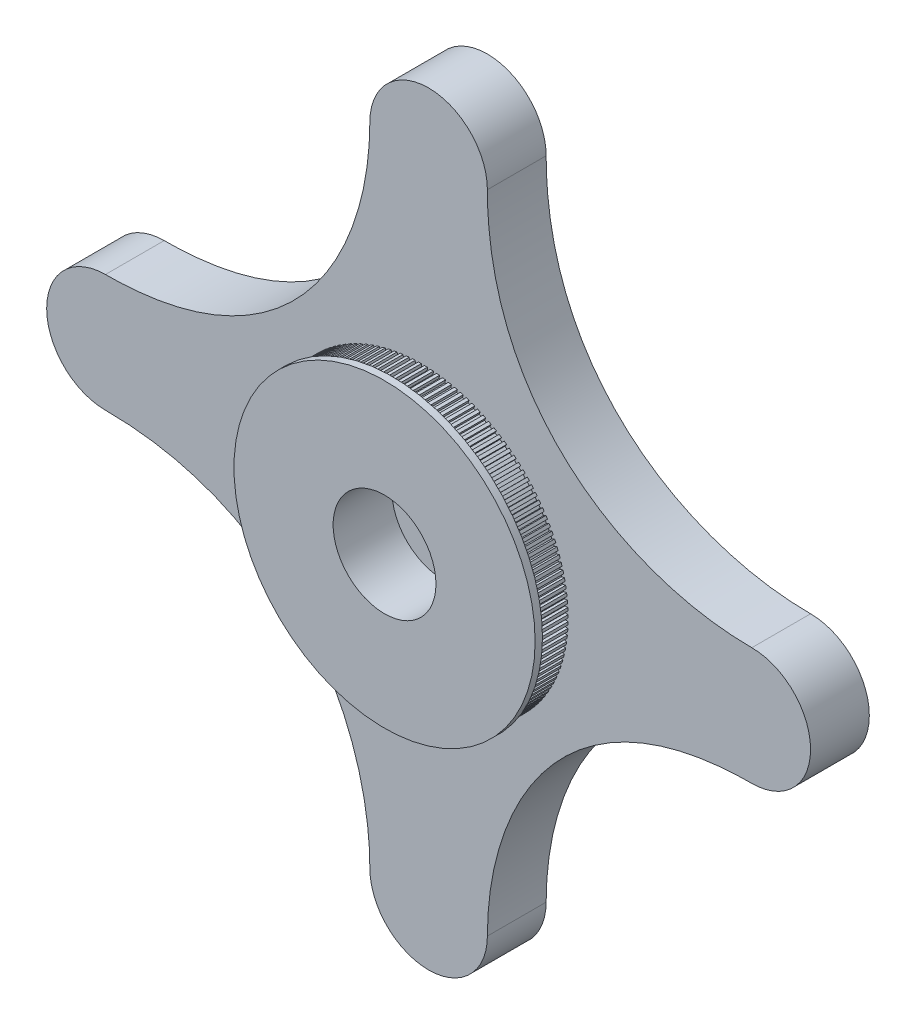
SolidWorks part; units mm, degrees
ref_plane "Front Plane" through (0, 0, 0) normal (0, 0, 1) x (1, 0, 0)
ref_plane "Top Plane" through (0, 0, 0) normal (0, 1, 0) x (1, 0, 0)
ref_plane "Right Plane" through (0, 0, 0) normal (1, 0, 0) x (0, 0, -1)
sketch "Sketch1" plane through (0, 0, 0) normal (0, 0, 1) x (1, 0, 0)
  line L0 (0, -50) -> (0, 50) construction
  line L1 (-50, 0) -> (50, 0) construction
  line L2 (-50, 0) -> (-110, 0) construction
  line L3 (0, 50) -> (0, 110) construction
  line L6 (50, 0) -> (90, 0) construction
  line L7 (0, -50) -> (0, -110) construction
  arc A6 (-20, -110) -> (20, -110) centre (0, -110) ccw
  arc A7 (20, 110) -> (-20, 110) centre (0, 110) ccw
  arc A8 (110, -20) -> (110, 20) centre (110, 0) ccw
  arc A9 (-110, 20) -> (-110, -20) centre (-110, 0) ccw
  spline S0 degree 3 poles (110, -20) (47.4794, -20) (20, -67.5736) (20, -110) knots 0 0 0 0 1 1 1 1
  spline S1 degree 3 poles (110, 20) (67.5736, 20) (20, 47.4794) (20, 110) knots 0 0 0 0 1 1 1 1
  spline S2 degree 3 poles (-20, 110) (-20, 67.5736) (-47.4794, 20) (-110, 20) knots 0 0 0 0 1 1 1 1
  spline S4 degree 3 poles (-110, -20) (-47.4794, -20) (-20, -67.5736) (-20, -110) knots 0 0 0 0 1 1 1 1
  dimension "D1" = 40
  dimension "D2" = 40
  dimension "D3" = 40
  dimension "D4" = 60
extrude "Boss-Extrude4" add sketch "Sketch1" along normal blind 20
sketch "Sketch5" plane through (0, 0, 0) normal (0, 0, -1) x (-1, 0, 0)
  circle A0 centre (0, 110) radius 7.5
  circle A1 centre (-110, 0) radius 7.5
  circle A2 centre (0, -110) radius 7.5
  circle A3 centre (110, 0) radius 7.5
  dimension "D1" = 15
extrude "Boss-Extrude5" add sketch "Sketch5" along normal blind 2.5
sketch "Sketch6" plane through (0, 0, 20) normal (0, 0, 1) x (1, 0, 0)
  circle A1 centre (0, 0) radius 45
  dimension "D2" = 90
extrude "Boss-Extrude7" add sketch "Sketch6" along normal blind 2.5
sketch "Sketch7" plane through (0, 0, 22.5) normal (0, 0, 1) x (1, 0, 0)
  circle A0 centre (0, 0) radius 50
  dimension "D1" = 100
extrude "Boss-Extrude8" add sketch "Sketch7" along normal blind 10
sketch "Sketch11" plane through (0, 0, 32.5) normal (0, 0, 1) x (1, 0, 0)
  line L0 (0, -49) -> (0, -49.9941)
  line L1 (1, -49.9841) -> (1, -48.9898)
  line L2 (-1.0664, -49.9828) -> (-2.066, -49.9514)
  line L3 (1, -49.9841) -> (0, -49.9941)
  line L4 (-1.0664, -49.9828) -> (-1.0254, -48.9893)
  line L5 (-2.0249, -48.9581) -> (-2.066, -49.9514)
  line L6 (-3.1311, -49.896) -> (-4.1285, -49.8234)
  line L7 (-3.1311, -49.896) -> (-3.049, -48.905)
  line L8 (-4.0464, -48.8326) -> (-4.1285, -49.8234)
  line L9 (-5.1903, -49.724) -> (-6.1839, -49.6102)
  line L10 (-5.1903, -49.724) -> (-5.0674, -48.7373)
  line L11 (-6.0609, -48.6237) -> (-6.1839, -49.6102)
  line L12 (-7.2408, -49.467) -> (-8.2288, -49.3123)
  line L13 (-7.2408, -49.467) -> (-7.0771, -48.4862)
  line L14 (-8.0651, -48.3317) -> (-8.2288, -49.3123)
  line L15 (-9.2788, -49.1255) -> (-10.2596, -48.9301)
  line L16 (-9.2788, -49.1255) -> (-9.0747, -48.1524)
  line L17 (-10.0556, -47.9571) -> (-10.2596, -48.9301)
  line L18 (-11.301, -48.7001) -> (-12.2728, -48.4643)
  line L19 (-11.301, -48.7001) -> (-11.0569, -47.7362)
  line L20 (-12.0288, -47.5006) -> (-12.2728, -48.4643)
  line L21 (-13.3039, -48.1915) -> (-14.2651, -47.9158)
  line L22 (-13.3039, -48.1915) -> (-13.0201, -47.2385)
  line L23 (-13.9815, -46.9629) -> (-14.2651, -47.9158)
  line L24 (-15.284, -47.6006) -> (-16.2331, -47.2853)
  line L25 (-15.284, -47.6006) -> (-14.9611, -46.6601)
  line L26 (-15.9103, -46.345) -> (-16.2331, -47.2853)
  line L27 (-17.238, -46.9283) -> (-18.1733, -46.5741)
  line L28 (-17.238, -46.9283) -> (-16.8766, -46.002)
  line L29 (-17.8119, -45.648) -> (-18.1733, -46.5741)
  line L30 (-19.1626, -46.1758) -> (-20.0824, -45.7833)
  line L31 (-19.1626, -46.1758) -> (-18.7632, -45.2652)
  line L32 (-19.6831, -44.8729) -> (-20.0824, -45.7833)
  line L33 (-21.0545, -45.3445) -> (-21.9573, -44.9143)
  line L34 (-21.0545, -45.3445) -> (-20.6178, -44.4512)
  line L35 (-21.5206, -44.0212) -> (-21.9573, -44.9143)
  line L36 (-22.9103, -44.4357) -> (-23.7946, -43.9685)
  line L37 (-22.9103, -44.4357) -> (-22.4371, -43.5612)
  line L38 (-23.3214, -43.0942) -> (-23.7946, -43.9685)
  line L39 (-24.7271, -43.451) -> (-25.5912, -42.9477)
  line L40 (-24.7271, -43.451) -> (-24.2181, -42.5968)
  line L41 (-25.0824, -42.0936) -> (-25.5912, -42.9477)
  line L42 (-26.5016, -42.392) -> (-27.3442, -41.8534)
  line L43 (-26.5016, -42.392) -> (-25.9577, -41.5596)
  line L44 (-26.8005, -41.0212) -> (-27.3442, -41.8534)
  line L45 (-28.2308, -41.2606) -> (-29.0504, -40.6877)
  line L46 (-28.2308, -41.2606) -> (-27.653, -40.4514)
  line L47 (-28.4728, -39.8786) -> (-29.0504, -40.6877)
  line L48 (-29.9117, -40.0587) -> (-30.707, -39.4524)
  line L49 (-29.9117, -40.0587) -> (-29.301, -39.274)
  line L50 (-30.0964, -38.6679) -> (-30.707, -39.4524)
  line L51 (-31.5416, -38.7884) -> (-32.3112, -38.1497)
  line L52 (-31.5416, -38.7884) -> (-30.899, -38.0296)
  line L53 (-31.6687, -37.3911) -> (-32.3112, -38.1497)
  line L54 (-33.1176, -37.4518) -> (-33.8601, -36.7819)
  line L55 (-33.1176, -37.4518) -> (-32.4442, -36.7202)
  line L56 (-33.1868, -36.0505) -> (-33.8601, -36.7819)
  line L57 (-34.637, -36.0512) -> (-35.3512, -35.3512)
  line L58 (-34.637, -36.0512) -> (-33.9339, -35.3481)
  line L59 (-34.6482, -34.6482) -> (-35.3512, -35.3512)
  line L60 (-36.0972, -34.5891) -> (-36.7819, -33.8601)
  line L61 (-36.0972, -34.5891) -> (-35.3657, -33.9156)
  line L62 (-36.0505, -33.1868) -> (-36.7819, -33.8601)
  line L63 (-37.4958, -33.0678) -> (-38.1497, -32.3112)
  line L64 (-37.4958, -33.0678) -> (-36.737, -32.4252)
  line L65 (-37.3911, -31.6687) -> (-38.1497, -32.3112)
  line L66 (-38.8303, -31.49) -> (-39.4524, -30.707)
  line L67 (-38.8303, -31.49) -> (-38.0456, -30.8793)
  line L68 (-38.6679, -30.0964) -> (-39.4524, -30.707)
  line L69 (-40.0984, -29.8585) -> (-40.6877, -29.0504)
  line L70 (-40.0984, -29.8585) -> (-39.2892, -29.2807)
  line L71 (-39.8786, -28.4728) -> (-40.6877, -29.0504)
  line L72 (-41.2981, -28.1759) -> (-41.8534, -27.3442)
  line L73 (-41.2981, -28.1759) -> (-40.4657, -27.632)
  line L74 (-41.0212, -26.8005) -> (-41.8534, -27.3442)
  line L75 (-42.4272, -26.4452) -> (-42.9477, -25.5912)
  line L76 (-42.4272, -26.4452) -> (-41.573, -25.9362)
  line L77 (-42.0936, -25.0824) -> (-42.9477, -25.5912)
  line L78 (-43.4838, -24.6693) -> (-43.9685, -23.7946)
  line L79 (-43.4838, -24.6693) -> (-42.6093, -24.196)
  line L80 (-43.0942, -23.3214) -> (-43.9685, -23.7946)
  line L81 (-44.4661, -22.8513) -> (-44.9143, -21.9573)
  line L82 (-44.4661, -22.8513) -> (-43.5728, -22.4145)
  line L83 (-44.0212, -21.5206) -> (-44.9143, -21.9573)
  line L84 (-45.3724, -20.9942) -> (-45.7833, -20.0824)
  line L85 (-45.3724, -20.9942) -> (-44.4619, -20.5947)
  line L86 (-44.8729, -19.6831) -> (-45.7833, -20.0824)
  line L87 (-46.2013, -19.1012) -> (-46.5741, -18.1733)
  line L88 (-46.2013, -19.1012) -> (-45.2749, -18.7398)
  line L89 (-45.648, -17.8119) -> (-46.5741, -18.1733)
  line L90 (-46.9512, -17.1756) -> (-47.2853, -16.2331)
  line L91 (-46.9512, -17.1756) -> (-46.0107, -16.8528)
  line L92 (-46.345, -15.9103) -> (-47.2853, -16.2331)
  line L93 (-47.6208, -15.2207) -> (-47.9158, -14.2651)
  line L94 (-47.6208, -15.2207) -> (-46.6678, -14.937)
  line L95 (-46.9629, -13.9815) -> (-47.9158, -14.2651)
  line L96 (-48.2091, -13.2398) -> (-48.4643, -12.2728)
  line L97 (-48.2091, -13.2398) -> (-47.2452, -12.9957)
  line L98 (-47.5006, -12.0288) -> (-48.4643, -12.2728)
  line L99 (-48.7151, -11.2362) -> (-48.9301, -10.2596)
  line L100 (-48.7151, -11.2362) -> (-47.7419, -11.0322)
  line L101 (-47.9571, -10.0556) -> (-48.9301, -10.2596)
  line L102 (-49.1378, -9.2135) -> (-49.3123, -8.2288)
  line L103 (-49.1378, -9.2135) -> (-48.157, -9.0498)
  line L104 (-48.3317, -8.0651) -> (-49.3123, -8.2288)
  line L105 (-49.4766, -7.175) -> (-49.6102, -6.1839)
  line L106 (-49.4766, -7.175) -> (-48.4899, -7.052)
  line L107 (-48.6237, -6.0609) -> (-49.6102, -6.1839)
  line L108 (-49.7308, -5.1242) -> (-49.8234, -4.1285)
  line L109 (-49.7308, -5.1242) -> (-48.7399, -5.0421)
  line L110 (-48.8326, -4.0464) -> (-49.8234, -4.1285)
  line L111 (-49.9001, -3.0647) -> (-49.9514, -2.066)
  line L112 (-49.9001, -3.0647) -> (-48.9066, -3.0236)
  line L113 (-48.9581, -2.0249) -> (-49.9514, -2.066)
  line L114 (-49.9841, -1) -> (-49.9941, 0)
  line L115 (-49.9841, -1) -> (-48.9898, -1)
  line L116 (-49, 0) -> (-49.9941, 0)
  line L117 (-49.9828, 1.0664) -> (-49.9514, 2.066)
  line L118 (-49.9828, 1.0664) -> (-48.9893, 1.0254)
  line L119 (-48.9581, 2.0249) -> (-49.9514, 2.066)
  line L120 (-49.896, 3.1311) -> (-49.8234, 4.1285)
  line L121 (-49.896, 3.1311) -> (-48.905, 3.049)
  line L122 (-48.8326, 4.0464) -> (-49.8234, 4.1285)
  line L123 (-49.724, 5.1903) -> (-49.6102, 6.1839)
  line L124 (-49.724, 5.1903) -> (-48.7373, 5.0674)
  line L125 (-48.6237, 6.0609) -> (-49.6102, 6.1839)
  line L126 (-49.467, 7.2408) -> (-49.3123, 8.2288)
  line L127 (-49.467, 7.2408) -> (-48.4862, 7.0771)
  line L128 (-48.3317, 8.0651) -> (-49.3123, 8.2288)
  line L129 (-49.1255, 9.2788) -> (-48.9301, 10.2596)
  line L130 (-49.1255, 9.2788) -> (-48.1524, 9.0747)
  line L131 (-47.9571, 10.0556) -> (-48.9301, 10.2596)
  line L132 (-48.7001, 11.301) -> (-48.4643, 12.2728)
  line L133 (-48.7001, 11.301) -> (-47.7362, 11.0569)
  line L134 (-47.5006, 12.0288) -> (-48.4643, 12.2728)
  line L135 (-48.1915, 13.3039) -> (-47.9158, 14.2651)
  line L136 (-48.1915, 13.3039) -> (-47.2385, 13.0201)
  line L137 (-46.9629, 13.9815) -> (-47.9158, 14.2651)
  line L138 (-47.6006, 15.284) -> (-47.2853, 16.2331)
  line L139 (-47.6006, 15.284) -> (-46.6601, 14.9611)
  line L140 (-46.345, 15.9103) -> (-47.2853, 16.2331)
  line L141 (-46.9283, 17.238) -> (-46.5741, 18.1733)
  line L142 (-46.9283, 17.238) -> (-46.002, 16.8766)
  line L143 (-45.648, 17.8119) -> (-46.5741, 18.1733)
  line L144 (-46.1758, 19.1626) -> (-45.7833, 20.0824)
  line L145 (-46.1758, 19.1626) -> (-45.2652, 18.7632)
  line L146 (-44.8729, 19.6831) -> (-45.7833, 20.0824)
  line L147 (-45.3445, 21.0545) -> (-44.9143, 21.9573)
  line L148 (-45.3445, 21.0545) -> (-44.4512, 20.6178)
  line L149 (-44.0212, 21.5206) -> (-44.9143, 21.9573)
  line L150 (-44.4357, 22.9103) -> (-43.9685, 23.7946)
  line L151 (-44.4357, 22.9103) -> (-43.5612, 22.4371)
  line L152 (-43.0942, 23.3214) -> (-43.9685, 23.7946)
  line L153 (-43.451, 24.7271) -> (-42.9477, 25.5912)
  line L154 (-43.451, 24.7271) -> (-42.5968, 24.2181)
  line L155 (-42.0936, 25.0824) -> (-42.9477, 25.5912)
  line L156 (-42.392, 26.5016) -> (-41.8534, 27.3442)
  line L157 (-42.392, 26.5016) -> (-41.5596, 25.9577)
  line L158 (-41.0212, 26.8005) -> (-41.8534, 27.3442)
  line L159 (-41.2606, 28.2308) -> (-40.6877, 29.0504)
  line L160 (-41.2606, 28.2308) -> (-40.4514, 27.653)
  line L161 (-39.8786, 28.4728) -> (-40.6877, 29.0504)
  line L162 (-40.0587, 29.9117) -> (-39.4524, 30.707)
  line L163 (-40.0587, 29.9117) -> (-39.274, 29.301)
  line L164 (-38.6679, 30.0964) -> (-39.4524, 30.707)
  line L165 (-38.7884, 31.5416) -> (-38.1497, 32.3112)
  line L166 (-38.7884, 31.5416) -> (-38.0296, 30.899)
  line L167 (-37.3911, 31.6687) -> (-38.1497, 32.3112)
  line L168 (-37.4518, 33.1176) -> (-36.7819, 33.8601)
  line L169 (-37.4518, 33.1176) -> (-36.7202, 32.4442)
  line L170 (-36.0505, 33.1868) -> (-36.7819, 33.8601)
  line L171 (-36.0512, 34.637) -> (-35.3512, 35.3512)
  line L172 (-36.0512, 34.637) -> (-35.3481, 33.9339)
  line L173 (-34.6482, 34.6482) -> (-35.3512, 35.3512)
  line L174 (-34.5891, 36.0972) -> (-33.8601, 36.7819)
  line L175 (-34.5891, 36.0972) -> (-33.9156, 35.3657)
  line L176 (-33.1868, 36.0505) -> (-33.8601, 36.7819)
  line L177 (-33.0678, 37.4958) -> (-32.3112, 38.1497)
  line L178 (-33.0678, 37.4958) -> (-32.4252, 36.737)
  line L179 (-31.6687, 37.3911) -> (-32.3112, 38.1497)
  line L180 (-31.49, 38.8303) -> (-30.707, 39.4524)
  line L181 (-31.49, 38.8303) -> (-30.8793, 38.0456)
  line L182 (-30.0964, 38.6679) -> (-30.707, 39.4524)
  line L183 (-29.8585, 40.0984) -> (-29.0504, 40.6877)
  line L184 (-29.8585, 40.0984) -> (-29.2807, 39.2892)
  line L185 (-28.4728, 39.8786) -> (-29.0504, 40.6877)
  line L186 (-28.1759, 41.2981) -> (-27.3442, 41.8534)
  line L187 (-28.1759, 41.2981) -> (-27.632, 40.4657)
  line L188 (-26.8005, 41.0212) -> (-27.3442, 41.8534)
  line L189 (-26.4452, 42.4272) -> (-25.5912, 42.9477)
  line L190 (-26.4452, 42.4272) -> (-25.9362, 41.573)
  line L191 (-25.0824, 42.0936) -> (-25.5912, 42.9477)
  line L192 (-24.6693, 43.4838) -> (-23.7946, 43.9685)
  line L193 (-24.6693, 43.4838) -> (-24.196, 42.6093)
  line L194 (-23.3214, 43.0942) -> (-23.7946, 43.9685)
  line L195 (-22.8513, 44.4661) -> (-21.9573, 44.9143)
  line L196 (-22.8513, 44.4661) -> (-22.4145, 43.5728)
  line L197 (-21.5206, 44.0212) -> (-21.9573, 44.9143)
  line L198 (-20.9942, 45.3724) -> (-20.0824, 45.7833)
  line L199 (-20.9942, 45.3724) -> (-20.5947, 44.4619)
  line L200 (-19.6831, 44.8729) -> (-20.0824, 45.7833)
  line L201 (-19.1012, 46.2013) -> (-18.1733, 46.5741)
  line L202 (-19.1012, 46.2013) -> (-18.7398, 45.2749)
  line L203 (-17.8119, 45.648) -> (-18.1733, 46.5741)
  line L204 (-17.1756, 46.9512) -> (-16.2331, 47.2853)
  line L205 (-17.1756, 46.9512) -> (-16.8528, 46.0107)
  line L206 (-15.9103, 46.345) -> (-16.2331, 47.2853)
  line L207 (-15.2207, 47.6208) -> (-14.2651, 47.9158)
  line L208 (-15.2207, 47.6208) -> (-14.937, 46.6678)
  line L209 (-13.9815, 46.9629) -> (-14.2651, 47.9158)
  line L210 (-13.2398, 48.2091) -> (-12.2728, 48.4643)
  line L211 (-13.2398, 48.2091) -> (-12.9957, 47.2452)
  line L212 (-12.0288, 47.5006) -> (-12.2728, 48.4643)
  line L213 (-11.2362, 48.7151) -> (-10.2596, 48.9301)
  line L214 (-11.2362, 48.7151) -> (-11.0322, 47.7419)
  line L215 (-10.0556, 47.9571) -> (-10.2596, 48.9301)
  line L216 (-9.2135, 49.1378) -> (-8.2288, 49.3123)
  line L217 (-9.2135, 49.1378) -> (-9.0498, 48.157)
  line L218 (-8.0651, 48.3317) -> (-8.2288, 49.3123)
  line L219 (-7.175, 49.4766) -> (-6.1839, 49.6102)
  line L220 (-7.175, 49.4766) -> (-7.052, 48.4899)
  line L221 (-6.0609, 48.6237) -> (-6.1839, 49.6102)
  line L222 (-5.1242, 49.7308) -> (-4.1285, 49.8234)
  line L223 (-5.1242, 49.7308) -> (-5.0421, 48.7399)
  line L224 (-4.0464, 48.8326) -> (-4.1285, 49.8234)
  line L225 (-3.0647, 49.9001) -> (-2.066, 49.9514)
  line L226 (-3.0647, 49.9001) -> (-3.0236, 48.9066)
  line L227 (-2.0249, 48.9581) -> (-2.066, 49.9514)
  line L228 (-1, 49.9841) -> (0, 49.9941)
  line L229 (-1, 49.9841) -> (-1, 48.9898)
  line L230 (0, 49) -> (0, 49.9941)
  line L231 (1.0664, 49.9828) -> (2.066, 49.9514)
  line L232 (1.0664, 49.9828) -> (1.0254, 48.9893)
  line L233 (2.0249, 48.9581) -> (2.066, 49.9514)
  line L234 (3.1311, 49.896) -> (4.1285, 49.8234)
  line L235 (3.1311, 49.896) -> (3.049, 48.905)
  line L236 (4.0464, 48.8326) -> (4.1285, 49.8234)
  line L237 (5.1903, 49.724) -> (6.1839, 49.6102)
  line L238 (5.1903, 49.724) -> (5.0674, 48.7373)
  line L239 (6.0609, 48.6237) -> (6.1839, 49.6102)
  line L240 (7.2408, 49.467) -> (8.2288, 49.3123)
  line L241 (7.2408, 49.467) -> (7.0771, 48.4862)
  line L242 (8.0651, 48.3317) -> (8.2288, 49.3123)
  line L243 (9.2788, 49.1255) -> (10.2596, 48.9301)
  line L244 (9.2788, 49.1255) -> (9.0747, 48.1524)
  line L245 (10.0556, 47.9571) -> (10.2596, 48.9301)
  line L246 (11.301, 48.7001) -> (12.2728, 48.4643)
  line L247 (11.301, 48.7001) -> (11.0569, 47.7362)
  line L248 (12.0288, 47.5006) -> (12.2728, 48.4643)
  line L249 (13.3039, 48.1915) -> (14.2651, 47.9158)
  line L250 (13.3039, 48.1915) -> (13.0201, 47.2385)
  line L251 (13.9815, 46.9629) -> (14.2651, 47.9158)
  line L252 (15.284, 47.6006) -> (16.2331, 47.2853)
  line L253 (15.284, 47.6006) -> (14.9611, 46.6601)
  line L254 (15.9103, 46.345) -> (16.2331, 47.2853)
  line L255 (17.238, 46.9283) -> (18.1733, 46.5741)
  line L256 (17.238, 46.9283) -> (16.8766, 46.002)
  line L257 (17.8119, 45.648) -> (18.1733, 46.5741)
  line L258 (19.1626, 46.1758) -> (20.0824, 45.7833)
  line L259 (19.1626, 46.1758) -> (18.7632, 45.2652)
  line L260 (19.6831, 44.8729) -> (20.0824, 45.7833)
  line L261 (21.0545, 45.3445) -> (21.9573, 44.9143)
  line L262 (21.0545, 45.3445) -> (20.6178, 44.4512)
  line L263 (21.5206, 44.0212) -> (21.9573, 44.9143)
  line L264 (22.9103, 44.4357) -> (23.7946, 43.9685)
  line L265 (22.9103, 44.4357) -> (22.4371, 43.5612)
  line L266 (23.3214, 43.0942) -> (23.7946, 43.9685)
  line L267 (24.7271, 43.451) -> (25.5912, 42.9477)
  line L268 (24.7271, 43.451) -> (24.2181, 42.5968)
  line L269 (25.0824, 42.0936) -> (25.5912, 42.9477)
  line L270 (26.5016, 42.392) -> (27.3442, 41.8534)
  line L271 (26.5016, 42.392) -> (25.9577, 41.5596)
  line L272 (26.8005, 41.0212) -> (27.3442, 41.8534)
  line L273 (28.2308, 41.2606) -> (29.0504, 40.6877)
  line L274 (28.2308, 41.2606) -> (27.653, 40.4514)
  line L275 (28.4728, 39.8786) -> (29.0504, 40.6877)
  line L276 (29.9117, 40.0587) -> (30.707, 39.4524)
  line L277 (29.9117, 40.0587) -> (29.301, 39.274)
  line L278 (30.0964, 38.6679) -> (30.707, 39.4524)
  line L279 (31.5416, 38.7884) -> (32.3112, 38.1497)
  line L280 (31.5416, 38.7884) -> (30.899, 38.0296)
  line L281 (31.6687, 37.3911) -> (32.3112, 38.1497)
  line L282 (33.1176, 37.4518) -> (33.8601, 36.7819)
  line L283 (33.1176, 37.4518) -> (32.4442, 36.7202)
  line L284 (33.1868, 36.0505) -> (33.8601, 36.7819)
  line L285 (34.637, 36.0512) -> (35.3512, 35.3512)
  line L286 (34.637, 36.0512) -> (33.9339, 35.3481)
  line L287 (34.6482, 34.6482) -> (35.3512, 35.3512)
  line L288 (36.0972, 34.5891) -> (36.7819, 33.8601)
  line L289 (36.0972, 34.5891) -> (35.3657, 33.9156)
  line L290 (36.0505, 33.1868) -> (36.7819, 33.8601)
  line L291 (37.4958, 33.0678) -> (38.1497, 32.3112)
  line L292 (37.4958, 33.0678) -> (36.737, 32.4252)
  line L293 (37.3911, 31.6687) -> (38.1497, 32.3112)
  line L294 (38.8303, 31.49) -> (39.4524, 30.707)
  line L295 (38.8303, 31.49) -> (38.0456, 30.8793)
  line L296 (38.6679, 30.0964) -> (39.4524, 30.707)
  line L297 (40.0984, 29.8585) -> (40.6877, 29.0504)
  line L298 (40.0984, 29.8585) -> (39.2892, 29.2807)
  line L299 (39.8786, 28.4728) -> (40.6877, 29.0504)
  line L300 (41.2981, 28.1759) -> (41.8534, 27.3442)
  line L301 (41.2981, 28.1759) -> (40.4657, 27.632)
  line L302 (41.0212, 26.8005) -> (41.8534, 27.3442)
  line L303 (42.4272, 26.4452) -> (42.9477, 25.5912)
  line L304 (42.4272, 26.4452) -> (41.573, 25.9362)
  line L305 (42.0936, 25.0824) -> (42.9477, 25.5912)
  line L306 (43.4838, 24.6693) -> (43.9685, 23.7946)
  line L307 (43.4838, 24.6693) -> (42.6093, 24.196)
  line L308 (43.0942, 23.3214) -> (43.9685, 23.7946)
  line L309 (44.4661, 22.8513) -> (44.9143, 21.9573)
  line L310 (44.4661, 22.8513) -> (43.5728, 22.4145)
  line L311 (44.0212, 21.5206) -> (44.9143, 21.9573)
  line L312 (45.3724, 20.9942) -> (45.7833, 20.0824)
  line L313 (45.3724, 20.9942) -> (44.4619, 20.5947)
  line L314 (44.8729, 19.6831) -> (45.7833, 20.0824)
  line L315 (46.2013, 19.1012) -> (46.5741, 18.1733)
  line L316 (46.2013, 19.1012) -> (45.2749, 18.7398)
  line L317 (45.648, 17.8119) -> (46.5741, 18.1733)
  line L318 (46.9512, 17.1756) -> (47.2853, 16.2331)
  line L319 (46.9512, 17.1756) -> (46.0107, 16.8528)
  line L320 (46.345, 15.9103) -> (47.2853, 16.2331)
  line L321 (47.6208, 15.2207) -> (47.9158, 14.2651)
  line L322 (47.6208, 15.2207) -> (46.6678, 14.937)
  line L323 (46.9629, 13.9815) -> (47.9158, 14.2651)
  line L324 (48.2091, 13.2398) -> (48.4643, 12.2728)
  line L325 (48.2091, 13.2398) -> (47.2452, 12.9957)
  line L326 (47.5006, 12.0288) -> (48.4643, 12.2728)
  line L327 (48.7151, 11.2362) -> (48.9301, 10.2596)
  line L328 (48.7151, 11.2362) -> (47.7419, 11.0322)
  line L329 (47.9571, 10.0556) -> (48.9301, 10.2596)
  line L330 (49.1378, 9.2135) -> (49.3123, 8.2288)
  line L331 (49.1378, 9.2135) -> (48.157, 9.0498)
  line L332 (48.3317, 8.0651) -> (49.3123, 8.2288)
  line L333 (49.4766, 7.175) -> (49.6102, 6.1839)
  line L334 (49.4766, 7.175) -> (48.4899, 7.052)
  line L335 (48.6237, 6.0609) -> (49.6102, 6.1839)
  line L336 (49.7308, 5.1242) -> (49.8234, 4.1285)
  line L337 (49.7308, 5.1242) -> (48.7399, 5.0421)
  line L338 (48.8326, 4.0464) -> (49.8234, 4.1285)
  line L339 (49.9001, 3.0647) -> (49.9514, 2.066)
  line L340 (49.9001, 3.0647) -> (48.9066, 3.0236)
  line L341 (48.9581, 2.0249) -> (49.9514, 2.066)
  line L342 (49.9841, 1) -> (49.9941, 0)
  line L343 (49.9841, 1) -> (48.9898, 1)
  line L344 (49, 0) -> (49.9941, 0)
  line L345 (49.9828, -1.0664) -> (49.9514, -2.066)
  line L346 (49.9828, -1.0664) -> (48.9893, -1.0254)
  line L347 (48.9581, -2.0249) -> (49.9514, -2.066)
  line L348 (49.896, -3.1311) -> (49.8234, -4.1285)
  line L349 (49.896, -3.1311) -> (48.905, -3.049)
  line L350 (48.8326, -4.0464) -> (49.8234, -4.1285)
  line L351 (49.724, -5.1903) -> (49.6102, -6.1839)
  line L352 (49.724, -5.1903) -> (48.7373, -5.0674)
  line L353 (48.6237, -6.0609) -> (49.6102, -6.1839)
  line L354 (49.467, -7.2408) -> (49.3123, -8.2288)
  line L355 (49.467, -7.2408) -> (48.4862, -7.0771)
  line L356 (48.3317, -8.0651) -> (49.3123, -8.2288)
  line L357 (49.1255, -9.2788) -> (48.9301, -10.2596)
  line L358 (49.1255, -9.2788) -> (48.1524, -9.0747)
  line L359 (47.9571, -10.0556) -> (48.9301, -10.2596)
  line L360 (48.7001, -11.301) -> (48.4643, -12.2728)
  line L361 (48.7001, -11.301) -> (47.7362, -11.0569)
  line L362 (47.5006, -12.0288) -> (48.4643, -12.2728)
  line L363 (48.1915, -13.3039) -> (47.9158, -14.2651)
  line L364 (48.1915, -13.3039) -> (47.2385, -13.0201)
  line L365 (46.9629, -13.9815) -> (47.9158, -14.2651)
  line L366 (47.6006, -15.284) -> (47.2853, -16.2331)
  line L367 (47.6006, -15.284) -> (46.6601, -14.9611)
  line L368 (46.345, -15.9103) -> (47.2853, -16.2331)
  line L369 (46.9283, -17.238) -> (46.5741, -18.1733)
  line L370 (46.9283, -17.238) -> (46.002, -16.8766)
  line L371 (45.648, -17.8119) -> (46.5741, -18.1733)
  line L372 (46.1758, -19.1626) -> (45.7833, -20.0824)
  line L373 (46.1758, -19.1626) -> (45.2652, -18.7632)
  line L374 (44.8729, -19.6831) -> (45.7833, -20.0824)
  line L375 (45.3445, -21.0545) -> (44.9143, -21.9573)
  line L376 (45.3445, -21.0545) -> (44.4512, -20.6178)
  line L377 (44.0212, -21.5206) -> (44.9143, -21.9573)
  line L378 (44.4357, -22.9103) -> (43.9685, -23.7946)
  line L379 (44.4357, -22.9103) -> (43.5612, -22.4371)
  line L380 (43.0942, -23.3214) -> (43.9685, -23.7946)
  line L381 (43.451, -24.7271) -> (42.9477, -25.5912)
  line L382 (43.451, -24.7271) -> (42.5968, -24.2181)
  line L383 (42.0936, -25.0824) -> (42.9477, -25.5912)
  line L384 (42.392, -26.5016) -> (41.8534, -27.3442)
  line L385 (42.392, -26.5016) -> (41.5596, -25.9577)
  line L386 (41.0212, -26.8005) -> (41.8534, -27.3442)
  line L387 (41.2606, -28.2308) -> (40.6877, -29.0504)
  line L388 (41.2606, -28.2308) -> (40.4514, -27.653)
  line L389 (39.8786, -28.4728) -> (40.6877, -29.0504)
  line L390 (40.0587, -29.9117) -> (39.4524, -30.707)
  line L391 (40.0587, -29.9117) -> (39.274, -29.301)
  line L392 (38.6679, -30.0964) -> (39.4524, -30.707)
  line L393 (38.7884, -31.5416) -> (38.1497, -32.3112)
  line L394 (38.7884, -31.5416) -> (38.0296, -30.899)
  line L395 (37.3911, -31.6687) -> (38.1497, -32.3112)
  line L396 (37.4518, -33.1176) -> (36.7819, -33.8601)
  line L397 (37.4518, -33.1176) -> (36.7202, -32.4442)
  line L398 (36.0505, -33.1868) -> (36.7819, -33.8601)
  line L399 (36.0512, -34.637) -> (35.3512, -35.3512)
  line L400 (36.0512, -34.637) -> (35.3481, -33.9339)
  line L401 (34.6482, -34.6482) -> (35.3512, -35.3512)
  line L402 (34.5891, -36.0972) -> (33.8601, -36.7819)
  line L403 (34.5891, -36.0972) -> (33.9156, -35.3657)
  line L404 (33.1868, -36.0505) -> (33.8601, -36.7819)
  line L405 (33.0678, -37.4958) -> (32.3112, -38.1497)
  line L406 (33.0678, -37.4958) -> (32.4252, -36.737)
  line L407 (31.6687, -37.3911) -> (32.3112, -38.1497)
  line L408 (31.49, -38.8303) -> (30.707, -39.4524)
  line L409 (31.49, -38.8303) -> (30.8793, -38.0456)
  line L410 (30.0964, -38.6679) -> (30.707, -39.4524)
  line L411 (29.8585, -40.0984) -> (29.0504, -40.6877)
  line L412 (29.8585, -40.0984) -> (29.2807, -39.2892)
  line L413 (28.4728, -39.8786) -> (29.0504, -40.6877)
  line L414 (28.1759, -41.2981) -> (27.3442, -41.8534)
  line L415 (28.1759, -41.2981) -> (27.632, -40.4657)
  line L416 (26.8005, -41.0212) -> (27.3442, -41.8534)
  line L417 (26.4452, -42.4272) -> (25.5912, -42.9477)
  line L418 (26.4452, -42.4272) -> (25.9362, -41.573)
  line L419 (25.0824, -42.0936) -> (25.5912, -42.9477)
  line L420 (24.6693, -43.4838) -> (23.7946, -43.9685)
  line L421 (24.6693, -43.4838) -> (24.196, -42.6093)
  line L422 (23.3214, -43.0942) -> (23.7946, -43.9685)
  line L423 (22.8513, -44.4661) -> (21.9573, -44.9143)
  line L424 (22.8513, -44.4661) -> (22.4145, -43.5728)
  line L425 (21.5206, -44.0212) -> (21.9573, -44.9143)
  line L426 (20.9942, -45.3724) -> (20.0824, -45.7833)
  line L427 (20.9942, -45.3724) -> (20.5947, -44.4619)
  line L428 (19.6831, -44.8729) -> (20.0824, -45.7833)
  line L429 (19.1012, -46.2013) -> (18.1733, -46.5741)
  line L430 (19.1012, -46.2013) -> (18.7398, -45.2749)
  line L431 (17.8119, -45.648) -> (18.1733, -46.5741)
  line L432 (17.1756, -46.9512) -> (16.2331, -47.2853)
  line L433 (17.1756, -46.9512) -> (16.8528, -46.0107)
  line L434 (15.9103, -46.345) -> (16.2331, -47.2853)
  line L435 (15.2207, -47.6208) -> (14.2651, -47.9158)
  line L436 (15.2207, -47.6208) -> (14.937, -46.6678)
  line L437 (13.9815, -46.9629) -> (14.2651, -47.9158)
  line L438 (13.2398, -48.2091) -> (12.2728, -48.4643)
  line L439 (13.2398, -48.2091) -> (12.9957, -47.2452)
  line L440 (12.0288, -47.5006) -> (12.2728, -48.4643)
  line L441 (11.2362, -48.7151) -> (10.2596, -48.9301)
  line L442 (11.2362, -48.7151) -> (11.0322, -47.7419)
  line L443 (10.0556, -47.9571) -> (10.2596, -48.9301)
  line L444 (9.2135, -49.1378) -> (8.2288, -49.3123)
  line L445 (9.2135, -49.1378) -> (9.0498, -48.157)
  line L446 (8.0651, -48.3317) -> (8.2288, -49.3123)
  line L447 (7.175, -49.4766) -> (6.1839, -49.6102)
  line L448 (7.175, -49.4766) -> (7.052, -48.4899)
  line L449 (6.0609, -48.6237) -> (6.1839, -49.6102)
  line L450 (5.1242, -49.7308) -> (4.1285, -49.8234)
  line L451 (5.1242, -49.7308) -> (5.0421, -48.7399)
  line L452 (4.0464, -48.8326) -> (4.1285, -49.8234)
  line L453 (3.0647, -49.9001) -> (2.066, -49.9514)
  line L454 (3.0647, -49.9001) -> (3.0236, -48.9066)
  line L455 (2.0249, -48.9581) -> (2.066, -49.9514)
  line L456 (1, -48.9898) -> (2.0249, -48.9581)
  line L457 (-1.0254, -48.9893) -> (0, -49)
  line L458 (-3.049, -48.905) -> (-2.0249, -48.9581)
  line L459 (-5.0674, -48.7373) -> (-4.0464, -48.8326)
  line L460 (-7.0771, -48.4862) -> (-6.0609, -48.6237)
  line L461 (-9.0747, -48.1524) -> (-8.0651, -48.3317)
  line L462 (-11.0569, -47.7362) -> (-10.0556, -47.9571)
  line L463 (-13.0201, -47.2385) -> (-12.0288, -47.5006)
  line L464 (-14.9611, -46.6601) -> (-13.9815, -46.9629)
  line L465 (-16.8766, -46.002) -> (-15.9103, -46.345)
  line L466 (-18.7632, -45.2652) -> (-17.8119, -45.648)
  line L467 (-20.6178, -44.4512) -> (-19.6831, -44.8729)
  line L468 (-22.4371, -43.5612) -> (-21.5206, -44.0212)
  line L469 (-24.2181, -42.5968) -> (-23.3214, -43.0942)
  line L470 (-25.9577, -41.5596) -> (-25.0824, -42.0936)
  line L471 (-27.653, -40.4514) -> (-26.8005, -41.0212)
  line L472 (-29.301, -39.274) -> (-28.4728, -39.8786)
  line L473 (-30.899, -38.0296) -> (-30.0964, -38.6679)
  line L474 (-32.4442, -36.7202) -> (-31.6687, -37.3911)
  line L475 (-33.9339, -35.3481) -> (-33.1868, -36.0505)
  line L476 (-35.3657, -33.9156) -> (-34.6482, -34.6482)
  line L477 (-36.737, -32.4252) -> (-36.0505, -33.1868)
  line L478 (-38.0456, -30.8793) -> (-37.3911, -31.6687)
  line L479 (-39.2892, -29.2807) -> (-38.6679, -30.0964)
  line L480 (-40.4657, -27.632) -> (-39.8786, -28.4728)
  line L481 (-41.573, -25.9362) -> (-41.0212, -26.8005)
  line L482 (-42.6093, -24.196) -> (-42.0936, -25.0824)
  line L483 (-43.5728, -22.4145) -> (-43.0942, -23.3214)
  line L484 (-44.4619, -20.5947) -> (-44.0212, -21.5206)
  line L485 (-45.2749, -18.7398) -> (-44.8729, -19.6831)
  line L486 (-46.0107, -16.8528) -> (-45.648, -17.8119)
  line L487 (-46.6678, -14.937) -> (-46.345, -15.9103)
  line L488 (-47.2452, -12.9957) -> (-46.9629, -13.9815)
  line L489 (-47.7419, -11.0322) -> (-47.5006, -12.0288)
  line L490 (-48.157, -9.0498) -> (-47.9571, -10.0556)
  line L491 (-48.4899, -7.052) -> (-48.3317, -8.0651)
  line L492 (-48.7399, -5.0421) -> (-48.6237, -6.0609)
  line L493 (-48.9066, -3.0236) -> (-48.8326, -4.0464)
  line L494 (-48.9898, -1) -> (-48.9581, -2.0249)
  line L495 (-48.9893, 1.0254) -> (-49, 0)
  line L496 (-48.905, 3.049) -> (-48.9581, 2.0249)
  line L497 (-48.7373, 5.0674) -> (-48.8326, 4.0464)
  line L498 (-48.4862, 7.0771) -> (-48.6237, 6.0609)
  line L499 (-48.1524, 9.0747) -> (-48.3317, 8.0651)
  line L500 (-47.7362, 11.0569) -> (-47.9571, 10.0556)
  line L501 (-47.2385, 13.0201) -> (-47.5006, 12.0288)
  line L502 (-46.6601, 14.9611) -> (-46.9629, 13.9815)
  line L503 (-46.002, 16.8766) -> (-46.345, 15.9103)
  line L504 (-45.2652, 18.7632) -> (-45.648, 17.8119)
  line L505 (-44.4512, 20.6178) -> (-44.8729, 19.6831)
  line L506 (-43.5612, 22.4371) -> (-44.0212, 21.5206)
  line L507 (-42.5968, 24.2181) -> (-43.0942, 23.3214)
  line L508 (-41.5596, 25.9577) -> (-42.0936, 25.0824)
  line L509 (-40.4514, 27.653) -> (-41.0212, 26.8005)
  line L510 (-39.274, 29.301) -> (-39.8786, 28.4728)
  line L511 (-38.0296, 30.899) -> (-38.6679, 30.0964)
  line L512 (-36.7202, 32.4442) -> (-37.3911, 31.6687)
  line L513 (-35.3481, 33.9339) -> (-36.0505, 33.1868)
  line L514 (-33.9156, 35.3657) -> (-34.6482, 34.6482)
  line L515 (-32.4252, 36.737) -> (-33.1868, 36.0505)
  line L516 (-30.8793, 38.0456) -> (-31.6687, 37.3911)
  line L517 (-29.2807, 39.2892) -> (-30.0964, 38.6679)
  line L518 (-27.632, 40.4657) -> (-28.4728, 39.8786)
  line L519 (-25.9362, 41.573) -> (-26.8005, 41.0212)
  line L520 (-24.196, 42.6093) -> (-25.0824, 42.0936)
  line L521 (-22.4145, 43.5728) -> (-23.3214, 43.0942)
  line L522 (-20.5947, 44.4619) -> (-21.5206, 44.0212)
  line L523 (-18.7398, 45.2749) -> (-19.6831, 44.8729)
  line L524 (-16.8528, 46.0107) -> (-17.8119, 45.648)
  line L525 (-14.937, 46.6678) -> (-15.9103, 46.345)
  line L526 (-12.9957, 47.2452) -> (-13.9815, 46.9629)
  line L527 (-11.0322, 47.7419) -> (-12.0288, 47.5006)
  line L528 (-9.0498, 48.157) -> (-10.0556, 47.9571)
  line L529 (-7.052, 48.4899) -> (-8.0651, 48.3317)
  line L530 (-5.0421, 48.7399) -> (-6.0609, 48.6237)
  line L531 (-3.0236, 48.9066) -> (-4.0464, 48.8326)
  line L532 (-1, 48.9898) -> (-2.0249, 48.9581)
  line L533 (1.0254, 48.9893) -> (0, 49)
  line L534 (3.049, 48.905) -> (2.0249, 48.9581)
  line L535 (5.0674, 48.7373) -> (4.0464, 48.8326)
  line L536 (7.0771, 48.4862) -> (6.0609, 48.6237)
  line L537 (9.0747, 48.1524) -> (8.0651, 48.3317)
  line L538 (11.0569, 47.7362) -> (10.0556, 47.9571)
  line L539 (13.0201, 47.2385) -> (12.0288, 47.5006)
  line L540 (14.9611, 46.6601) -> (13.9815, 46.9629)
  line L541 (16.8766, 46.002) -> (15.9103, 46.345)
  line L542 (18.7632, 45.2652) -> (17.8119, 45.648)
  line L543 (20.6178, 44.4512) -> (19.6831, 44.8729)
  line L544 (22.4371, 43.5612) -> (21.5206, 44.0212)
  line L545 (24.2181, 42.5968) -> (23.3214, 43.0942)
  line L546 (25.9577, 41.5596) -> (25.0824, 42.0936)
  line L547 (27.653, 40.4514) -> (26.8005, 41.0212)
  line L548 (29.301, 39.274) -> (28.4728, 39.8786)
  line L549 (30.899, 38.0296) -> (30.0964, 38.6679)
  line L550 (32.4442, 36.7202) -> (31.6687, 37.3911)
  line L551 (33.9339, 35.3481) -> (33.1868, 36.0505)
  line L552 (35.3657, 33.9156) -> (34.6482, 34.6482)
  line L553 (36.737, 32.4252) -> (36.0505, 33.1868)
  line L554 (38.0456, 30.8793) -> (37.3911, 31.6687)
  line L555 (39.2892, 29.2807) -> (38.6679, 30.0964)
  line L556 (40.4657, 27.632) -> (39.8786, 28.4728)
  line L557 (41.573, 25.9362) -> (41.0212, 26.8005)
  line L558 (42.6093, 24.196) -> (42.0936, 25.0824)
  line L559 (43.5728, 22.4145) -> (43.0942, 23.3214)
  line L560 (44.4619, 20.5947) -> (44.0212, 21.5206)
  line L561 (45.2749, 18.7398) -> (44.8729, 19.6831)
  line L562 (46.0107, 16.8528) -> (45.648, 17.8119)
  line L563 (46.6678, 14.937) -> (46.345, 15.9103)
  line L564 (47.2452, 12.9957) -> (46.9629, 13.9815)
  line L565 (47.7419, 11.0322) -> (47.5006, 12.0288)
  line L566 (48.157, 9.0498) -> (47.9571, 10.0556)
  line L567 (48.4899, 7.052) -> (48.3317, 8.0651)
  line L568 (48.7399, 5.0421) -> (48.6237, 6.0609)
  line L569 (48.9066, 3.0236) -> (48.8326, 4.0464)
  line L570 (48.9898, 1) -> (48.9581, 2.0249)
  line L571 (48.9893, -1.0254) -> (49, 0)
  line L572 (48.905, -3.049) -> (48.9581, -2.0249)
  line L573 (48.7373, -5.0674) -> (48.8326, -4.0464)
  line L574 (48.4862, -7.0771) -> (48.6237, -6.0609)
  line L575 (48.1524, -9.0747) -> (48.3317, -8.0651)
  line L576 (47.7362, -11.0569) -> (47.9571, -10.0556)
  line L577 (47.2385, -13.0201) -> (47.5006, -12.0288)
  line L578 (46.6601, -14.9611) -> (46.9629, -13.9815)
  line L579 (46.002, -16.8766) -> (46.345, -15.9103)
  line L580 (45.2652, -18.7632) -> (45.648, -17.8119)
  line L581 (44.4512, -20.6178) -> (44.8729, -19.6831)
  line L582 (43.5612, -22.4371) -> (44.0212, -21.5206)
  line L583 (42.5968, -24.2181) -> (43.0942, -23.3214)
  line L584 (41.5596, -25.9577) -> (42.0936, -25.0824)
  line L585 (40.4514, -27.653) -> (41.0212, -26.8005)
  line L586 (39.274, -29.301) -> (39.8786, -28.4728)
  line L587 (38.0296, -30.899) -> (38.6679, -30.0964)
  line L588 (36.7202, -32.4442) -> (37.3911, -31.6687)
  line L589 (35.3481, -33.9339) -> (36.0505, -33.1868)
  line L590 (33.9156, -35.3657) -> (34.6482, -34.6482)
  line L591 (32.4252, -36.737) -> (33.1868, -36.0505)
  line L592 (30.8793, -38.0456) -> (31.6687, -37.3911)
  line L593 (29.2807, -39.2892) -> (30.0964, -38.6679)
  line L594 (27.632, -40.4657) -> (28.4728, -39.8786)
  line L595 (25.9362, -41.573) -> (26.8005, -41.0212)
  line L596 (24.196, -42.6093) -> (25.0824, -42.0936)
  line L597 (22.4145, -43.5728) -> (23.3214, -43.0942)
  line L598 (20.5947, -44.4619) -> (21.5206, -44.0212)
  line L599 (18.7398, -45.2749) -> (19.6831, -44.8729)
  line L600 (16.8528, -46.0107) -> (17.8119, -45.648)
  line L601 (14.937, -46.6678) -> (15.9103, -46.345)
  line L602 (12.9957, -47.2452) -> (13.9815, -46.9629)
  line L603 (11.0322, -47.7419) -> (12.0288, -47.5006)
  line L604 (9.0498, -48.157) -> (10.0556, -47.9571)
  line L605 (7.052, -48.4899) -> (8.0651, -48.3317)
  line L606 (5.0421, -48.7399) -> (6.0609, -48.6237)
  line L607 (3.0236, -48.9066) -> (4.0464, -48.8326)
  circle A0 centre (0, 0) radius 49.9941 construction
  circle A1 centre (0, 0) radius 49 construction
  circle A2 centre (0, 0) radius 58.0298
  point P614 (0, 0)
  point P917 (0, 0)
  dimension "D1" = 98
  dimension "D2" = 152
  dimension "D3" = 1
  dimension "D4" = 152
extrude "Cut-Extrude3" cut sketch "Sketch11" against normal blind 10
sketch "Sketch9" plane through (0, 0, 32.5) normal (0, 0, 1) x (1, 0, 0)
  circle A0 centre (0, 0) radius 51.25
  dimension "D1" = 102.5
extrude "Boss-Extrude9" add sketch "Sketch9" along normal blind 2.5
sketch "Sketch10" plane through (0, 0, 35) normal (0, 0, 1) x (1, 0, 0)
  circle A0 centre (0, 0) radius 17.5
  dimension "D1" = 35
extrude "Cut-Extrude2" cut sketch "Sketch10" against normal blind 20
